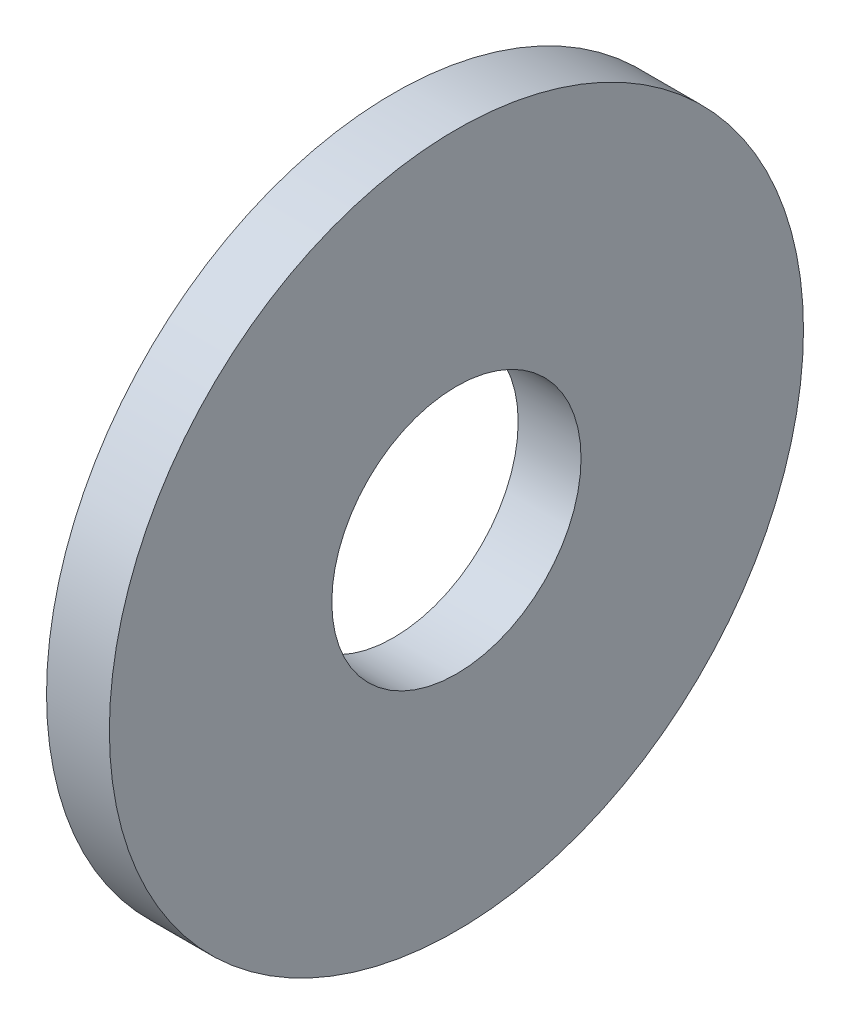
SolidWorks part; units mm, degrees
ref_plane "Plane1" through (0, 0, 0) normal (0, 0, 1) x (1, 0, 0)
ref_plane "Plane2" through (0, 0, 0) normal (0, 1, 0) x (1, 0, 0)
ref_plane "Plane3" through (0, 0, 0) normal (1, 0, 0) x (0, 0, -1)
sketch "Sketch1" plane through (0, 0, 0) normal (0, 0, 1) x (1, 0, 0)
  line L0 (-34.925, 0) -> (9.525, 0) construction
  line L1 (0, 4.56) -> (0, 12.7)
  line L2 (0, 12.7) -> (-2.3, 12.7)
  line L3 (-2.3, 12.7) -> (-2.3, 4.56)
  line L4 (-2.3, 4.56) -> (0, 4.56)
  dimension "Thickness" = 2.3
  dimension "Inside_dia" = 9.12
  dimension "Outside_dia" = 25.4
revolve "Base-Revolve" add sketch "Sketch1" angle 360 about L0
